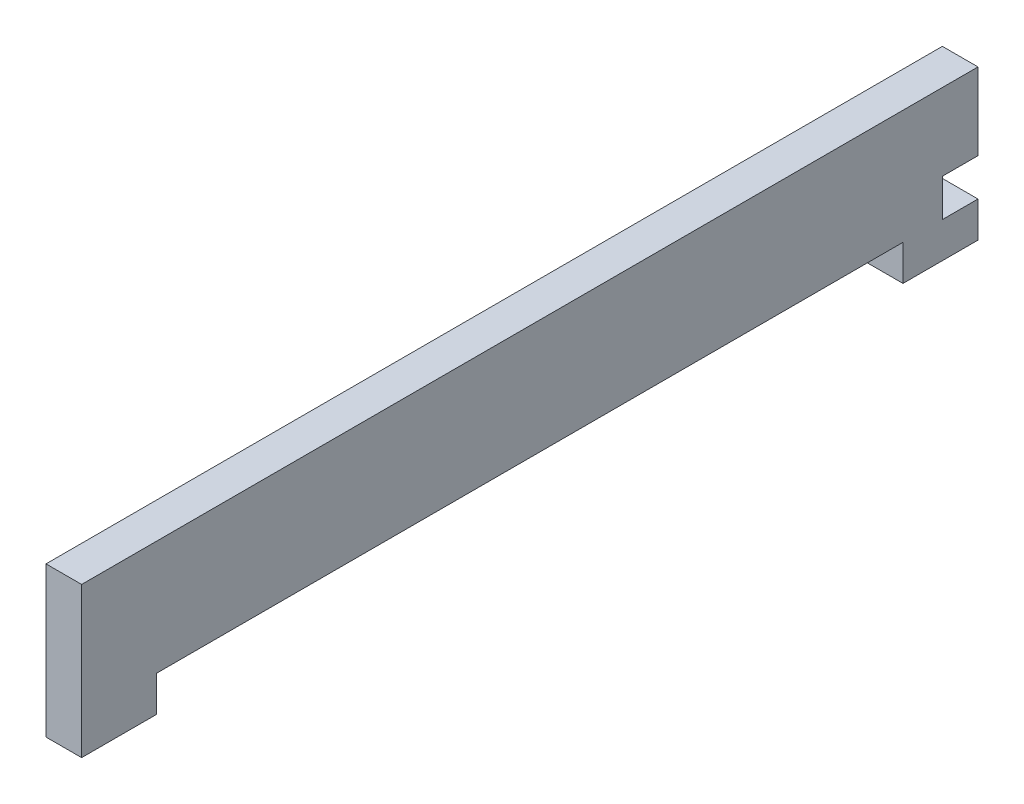
SolidWorks part; units mm, degrees
ref_plane "Front Plane" through (0, 0, 0) normal (0, 0, 1) x (1, 0, 0)
ref_plane "Top Plane" through (0, 0, 0) normal (0, 1, 0) x (1, 0, 0)
ref_plane "Right Plane" through (0, 0, 0) normal (1, 0, 0) x (0, 0, -1)
sketch "Sketch1" plane through (0, 0, 0) normal (1, 0, 0) x (0, 0, -1)
  line L0 (109.5, 0) -> (119.5, 0)
  line L1 (0, 0) -> (10, 0)
  line L2 (0, 0) -> (0, 20)
  line L3 (0, 20) -> (119.5, 20)
  line L4 (119.5, 0) -> (119.5, 20)
  line L6 (10, 0) -> (10, 4.75)
  line L7 (10, 4.75) -> (109.5, 4.75)
  line L8 (109.5, 0) -> (109.5, 4.75)
  dimension "D1" = 119.5
  dimension "D2" = 20
  dimension "D3" = 10
  dimension "D4" = 4.75
  dimension "D5" = 10
extrude "Boss-Extrude1" add sketch "Sketch1" along normal blind 4.75
sketch "Sketch2" plane through (4.75, 0, 0) normal (1, 0, 0) x (0, 0, -1)
  line L0 (119.5, 0) -> (119.5, 20) construction
  line L1 (119.5, 4.75) -> (114.75, 4.75)
  line L2 (119.5, 4.75) -> (119.5, 9.75)
  line L3 (119.5, 9.75) -> (114.75, 9.75)
  line L4 (114.75, 4.75) -> (114.75, 9.75)
  line L5 (10, 4.75) -> (109.5, 4.75) construction
  dimension "D1" = 4.75
  dimension "D2" = 5
extrude "Cut-Extrude1" cut sketch "Sketch2" against normal blind 4.75
